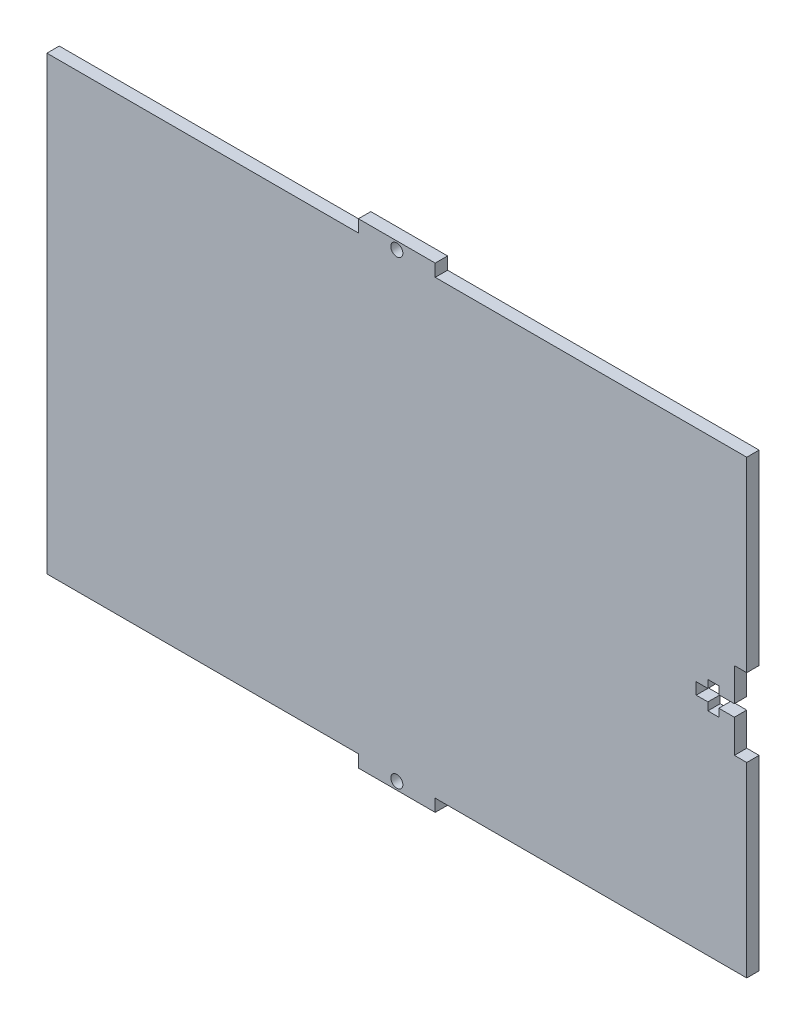
SolidWorks part; units mm, degrees
ref_plane "Front Plane" through (0, 0, 0) normal (0, 0, 1) x (1, 0, 0)
ref_plane "Top Plane" through (0, 0, 0) normal (0, 1, 0) x (1, 0, 0)
ref_plane "Right Plane" through (0, 0, 0) normal (1, 0, 0) x (0, 0, -1)
sketch "Sketch1" plane through (0, 0, 0) normal (0, 0, 1) x (1, 0, 0)
  line L1 (-90, 61.18) -> (90, 61.18)
  line L2 (-90, 61.18) -> (-90, -61.18)
  line L3 (-90, -61.18) -> (90, -61.18)
  line L4 (90, 61.18) -> (90, -61.18)
  dimension "D1" = 61.18
  dimension "D2" = 122.36
  dimension "D3" = 180
  dimension "D4" = 90
extrude "Boss-Extrude1" add sketch "Sketch1" along normal blind 3.18
sketch "Sketch2" plane through (0, 0, 3.18) normal (0, 0, 1) x (1, 0, 0)
  line L0 (0, 0) -> (77, 0) construction
  line L1 (0, 0) -> (0, -50000) construction
  line L4 (90, -61.18) -> (90, 61.18) construction
  line L5 (80, 1.5) -> (77, 1.5)
  line L6 (90, 10) -> (86.82, 10)
  line L7 (90, 10) -> (90, -10)
  line L8 (90, -10) -> (86.82, -10)
  line L9 (86.82, 10) -> (86.82, 1.5)
  line L10 (86.82, 1.5) -> (82.82, 1.5)
  line L12 (86.82, -1.5) -> (82.82, -1.5)
  line L13 (77, 1.5) -> (77, -1.5)
  line L14 (80, 3.5) -> (82.82, 3.5)
  line L15 (80, 3.5) -> (80, 1.5)
  line L16 (80, -3.5) -> (82.82, -3.5)
  line L17 (82.82, 3.5) -> (82.82, 1.5)
  line L18 (80, -1.5) -> (80, -3.5)
  line L19 (90, 0) -> (50000, 0) construction
  line L20 (80, -1.5) -> (77, -1.5)
  line L21 (82.82, -1.5) -> (82.82, -3.5)
  line L22 (86.82, -1.5) -> (86.82, -10)
  point P20 (0, 0)
  point P21 (0, 0)
  dimension "D1" = 3.18
  dimension "D2" = 20
  dimension "D3" = 10
  dimension "D4" = 9.82
  dimension "D5" = 3
  dimension "D6" = 1.5
  dimension "D7" = 2.82
  dimension "D8" = 3.5
  dimension "D9" = 7
  dimension "D10" = 3
extrude "Cut-Extrude1" cut sketch "Sketch2" against normal through all both and the other way through all
sketch "Sketch3" plane through (0, 0, 3.18) normal (0, 0, 1) x (1, 0, 0)
  line L0 (0, 0) -> (50000, 0) construction
  line L1 (0, 0) -> (0, -50000) construction
  line L3 (-90, -61.18) -> (-9.875, -61.18)
  line L4 (-90, -61.18) -> (-90, -58)
  line L5 (-90, -58) -> (-9.875, -58)
  line L6 (-9.875, -61.18) -> (-9.875, -58)
  line L7 (90, -61.18) -> (9.875, -61.18)
  line L8 (90, -61.18) -> (90, -58)
  line L9 (90, -58) -> (9.875, -58)
  line L10 (9.875, -61.18) -> (9.875, -58)
  dimension "D1" = 80.125
  dimension "D2" = 80.125
  dimension "D3" = 3.18
  dimension "D4" = 3.18
extrude "Cut-Extrude2" cut sketch "Sketch3" against normal through all both and the other way through all
mirror "Mirror1" about plane through (0, 0, 0) normal (0, 1, 0) of "Cut-Extrude2"
sketch "Sketch4" plane through (0, 0, 3.18) normal (0, 0, 1) x (1, 0, 0)
  line L0 (-9.875, -61.18) -> (9.875, -61.18) construction
  line L1 (9.875, -58) -> (9.875, -61.18) construction
  circle A0 centre (0, -59.18) radius 1.55
  dimension "D1" = 3.1
  dimension "D2" = 2
  dimension "D3" = 9.875
extrude "Cut-Extrude3" cut sketch "Sketch4" against normal through all both and the other way through all
mirror "Mirror2" about plane through (0, 0, 0) normal (0, 1, 0) of "Cut-Extrude3"
sketch "Sketch5" plane through (0, 0, 3.18) normal (0, 0, 1) x (1, 0, 0)
  line L0 (-86.82, 58) -> (-86.82, -49942) construction
  line L2 (-90, 58) -> (-90, -58) construction
  dimension "D1" = 3.18
